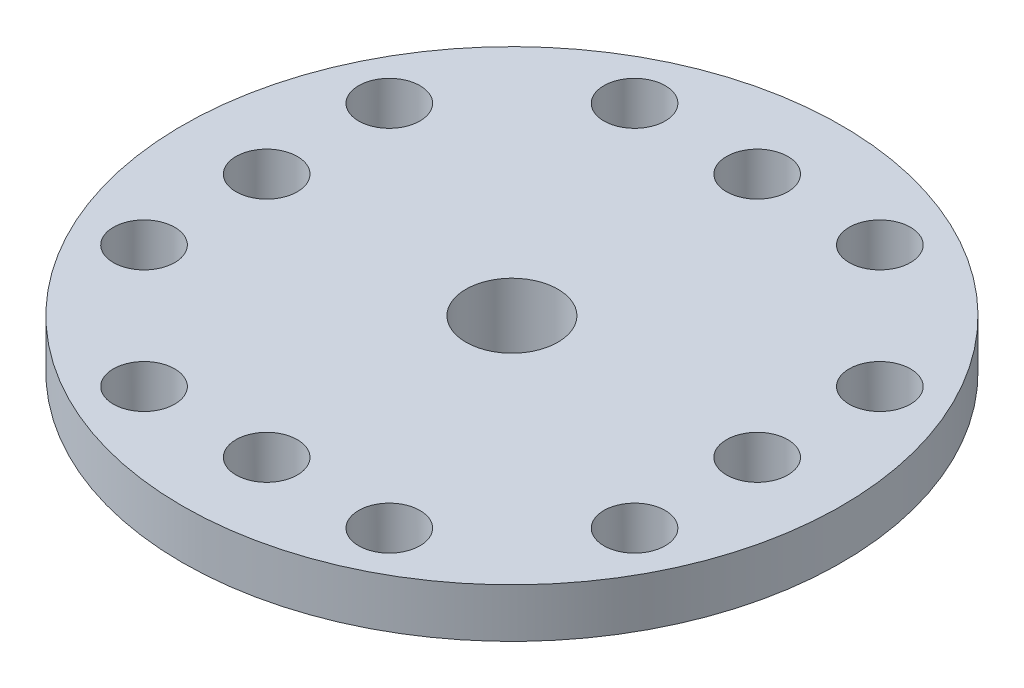
SolidWorks part; units mm, degrees
material "PA Type 6"
ref_plane "Front Plane" through (0, 0, 0) normal (0, 0, 1) x (1, 0, 0)
ref_plane "Top Plane" through (0, 0, 0) normal (0, 1, 0) x (1, 0, 0)
ref_plane "Right Plane" through (0, 0, 0) normal (1, 0, 0) x (0, 0, -1)
sketch "Sketch1" plane through (0, 0, 0) normal (0, 1, 0) x (1, 0, 0)
  circle A0 centre (0, 0) radius 6
  dimension "D1" = 12
extrude "Boss-Extrude1" add sketch "Sketch1" along normal blind 7.5
sketch "Sketch2" plane through (0, 7.5, 0) normal (0, 1, 0) x (1, 0, 0)
  circle A0 centre (0, 0) radius 21.5
  dimension "D1" = 43
extrude "Boss-Extrude2" add sketch "Sketch2" along normal blind 3.2
sketch "Sketch3" plane through (0, 10.7, 0) normal (0, 1, 0) x (1, 0, 0)
  line L0 (0, 29.3562) -> (0, 0) construction
  line L1 (0, 0) -> (31.2912, 0) construction
  line L2 (-8, 16) -> (8, 16) construction
  circle A0 centre (0, 16) radius 2
  circle A1 centre (8, 16) radius 2
  circle A2 centre (-8, 16) radius 2
  dimension "D1" = 32
  dimension "D2" = 4
  dimension "D3" = 16
extrude "Cut-Extrude1" cut sketch "Sketch3" against normal through all
sketch "Sketch4" plane through (0, 10.7, 0) normal (0, 1, 0) x (1, 0, 0)
  circle A0 centre (0, 0) radius 1.25
  dimension "D1" = 2.5
extrude "Cut-Extrude2" cut sketch "Sketch4" against normal through all
pattern_circular "CirPattern1" count 4 over 360 about axis through (0, 0, 0) along (0, 1, 0) of "Cut-Extrude1"
sketch "Sketch5" plane through (0, 10.7, 0) normal (0, 1, 0) x (1, 0, 0)
  circle A0 centre (0, 0) radius 3
  dimension "D1" = 6
extrude "Cut-Extrude3" cut sketch "Sketch5" against normal blind 6.2
sketch "Sketch6" plane through (0, 0, 0) normal (0, -1, 0) x (1, 0, 0)
  circle A0 centre (0, 0) radius 3
  dimension "D1" = 6
extrude "Cut-Extrude4" cut sketch "Sketch6" against normal blind 3.5
